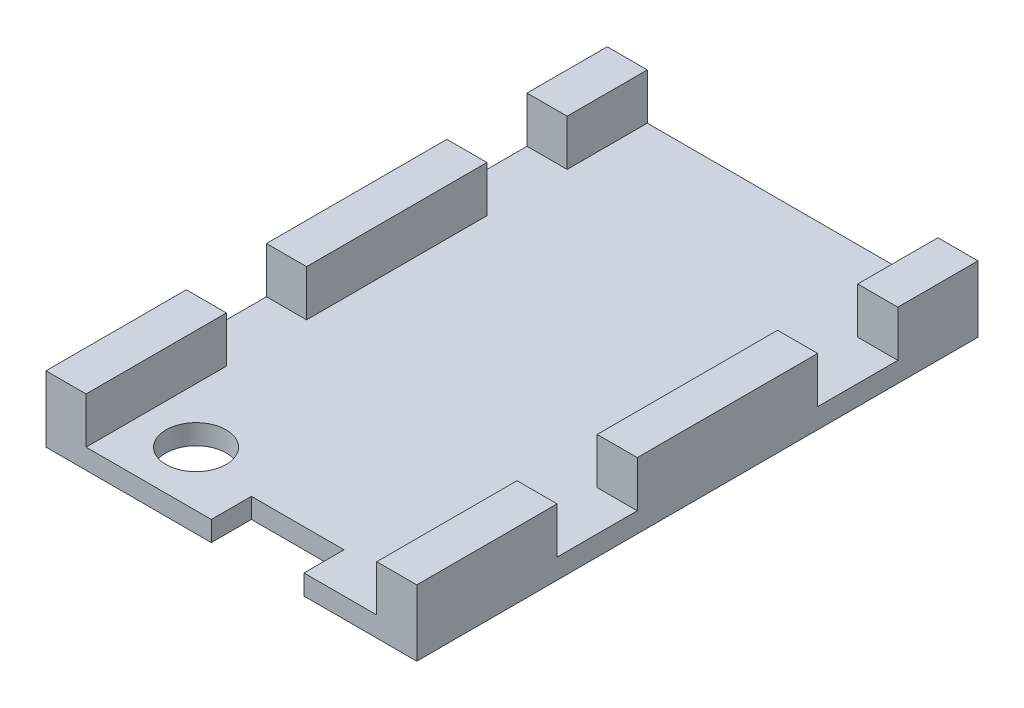
SolidWorks part; units mm, degrees
ref_plane "Front Plane" through (0, 0, 0) normal (0, 0, 1) x (1, 0, 0)
ref_plane "Top Plane" through (0, 0, 0) normal (0, 1, 0) x (1, 0, 0)
ref_plane "Right Plane" through (0, 0, 0) normal (1, 0, 0) x (0, 0, -1)
sketch "main board outline" plane through (0, 0, 0) normal (0, 1, 0) x (1, 0, 0)
  line L1 (-27.2474, 14.651) -> (-12.7474, 14.651)
  line L2 (-27.2474, 14.651) -> (-27.2474, -13.349)
  line L3 (-27.2474, -13.349) -> (-12.7474, -13.349)
  line L4 (-12.7474, 14.651) -> (-12.7474, -13.349)
  line L5 (-29.2474, 14.651) -> (-10.7474, 14.651)
  line L6 (-29.2474, 14.651) -> (-29.2474, -13.349)
  line L7 (-29.2474, -13.349) -> (-10.7474, -13.349)
  line L8 (-10.7474, 14.651) -> (-10.7474, -13.349)
  dimension "D1" = 28
  dimension "D2" = 14.5
  dimension "D3" = 2
  dimension "D4" = 2
extrude "side1" add sketch "main board outline" along normal blind 1 contours L6 L7 L8 L5
sketch "Sketch2" plane through (0, 1, 0) normal (0, 1, 0) x (1, 0, 0)
  line L0 (-29.2474, -13.349) -> (-10.7474, -13.349) construction
  line L1 (-29.2474, 14.651) -> (-27.2474, 14.651)
  line L2 (-29.2474, 14.651) -> (-29.2474, -13.349)
  line L3 (-29.2474, -13.349) -> (-27.2474, -13.349)
  line L4 (-27.2474, 14.651) -> (-27.2474, -13.349)
  line L6 (-10.7474, 14.651) -> (-12.7474, 14.651)
  line L7 (-10.7474, 14.651) -> (-10.7474, -13.349)
  line L8 (-10.7474, -13.349) -> (-12.7474, -13.349)
  line L9 (-12.7474, 14.651) -> (-12.7474, -13.349)
  dimension "D1" = 2
  dimension "D2" = 2
extrude "walls" add sketch "Sketch2" along normal blind 2.3
sketch "Sketch3" plane through (0, 0, 0) normal (0, -1, 0) x (-1, 0, 0)
  line L0 (29.2474, -13.349) -> (10.7474, -13.349) construction
  line L2 (29.2474, 14.651) -> (29.2474, -13.349) construction
  circle A0 centre (24.5044, -10.6058) radius 1.5
  dimension "D1" = 2.7432
  dimension "D2" = 4.743
extrude "screw hole" cut sketch "Sketch3" against normal blind 2.3
sketch "Sketch4" plane through (0, 0, 0) normal (0, -1, 0) x (-1, 0, 0)
  line L0 (29.2474, -13.349) -> (10.7474, -13.349) construction
  line L1 (16.3766, -13.349) -> (20.9994, -13.349)
  line L2 (16.3766, -13.349) -> (16.3766, -11.349)
  line L3 (16.3766, -11.349) -> (20.9994, -11.349)
  line L4 (20.9994, -13.349) -> (20.9994, -11.349)
  line L6 (29.2474, 14.651) -> (29.2474, -13.349) construction
  dimension "D1" = 4.6228
  dimension "D2" = 8.248
  dimension "D3" = 2
extrude "spi hole" cut sketch "Sketch4" against normal blind 2.3
sketch "Sketch5" plane through (0, 3.3, 0) normal (0, 1, 0) x (1, 0, 0)
  line L0 (-29.2474, 14.651) -> (-29.2474, -13.349) construction
  line L1 (-29.2474, 10.651) -> (-27.2474, 10.651)
  line L2 (-29.2474, 10.651) -> (-29.2474, 6.651)
  line L3 (-29.2474, 6.651) -> (-27.2474, 6.651)
  line L4 (-27.2474, 10.651) -> (-27.2474, 6.651)
  line L5 (-27.2474, -13.349) -> (-27.2474, 14.651) construction
  line L6 (-27.2474, -13.349) -> (-27.2474, 14.651) construction
  line L7 (-29.2474, -2.349) -> (-27.2474, -2.349)
  line L8 (-29.2474, -2.349) -> (-29.2474, -6.349)
  line L9 (-29.2474, -6.349) -> (-27.2474, -6.349)
  line L10 (-27.2474, -2.349) -> (-27.2474, -6.349)
  line L11 (-12.7474, 14.651) -> (-12.7474, -13.349) construction
  line L12 (-12.7474, 10.651) -> (-10.7474, 10.651)
  line L13 (-12.7474, 10.651) -> (-12.7474, 6.651)
  line L14 (-12.7474, 6.651) -> (-10.7474, 6.651)
  line L15 (-10.7474, 10.651) -> (-10.7474, 6.651)
  line L16 (-10.7474, -13.349) -> (-10.7474, 14.651) construction
  line L18 (-12.7474, -2.349) -> (-10.7474, -2.349)
  line L19 (-12.7474, -2.349) -> (-12.7474, -6.349)
  line L20 (-12.7474, -6.349) -> (-10.7474, -6.349)
  line L21 (-10.7474, -2.349) -> (-10.7474, -6.349)
  line L22 (-27.2474, 14.651) -> (-29.2474, 14.651) construction
  line L23 (-10.7474, 14.651) -> (-12.7474, 14.651) construction
  line L24 (-29.2474, -13.349) -> (-27.2474, -13.349) construction
  line L25 (-12.7474, -13.349) -> (-10.7474, -13.349) construction
  point P28 (-11.7474, 14.651)
  dimension "D1" = 4
  dimension "D2" = 4
  dimension "D3" = 4
  dimension "D4" = 4
  dimension "D5" = 4
  dimension "D6" = 4
  dimension "D7" = 7
  dimension "D8" = 7
extrude "Cut-Extrude3" cut sketch "Sketch5" against normal blind 2.3
